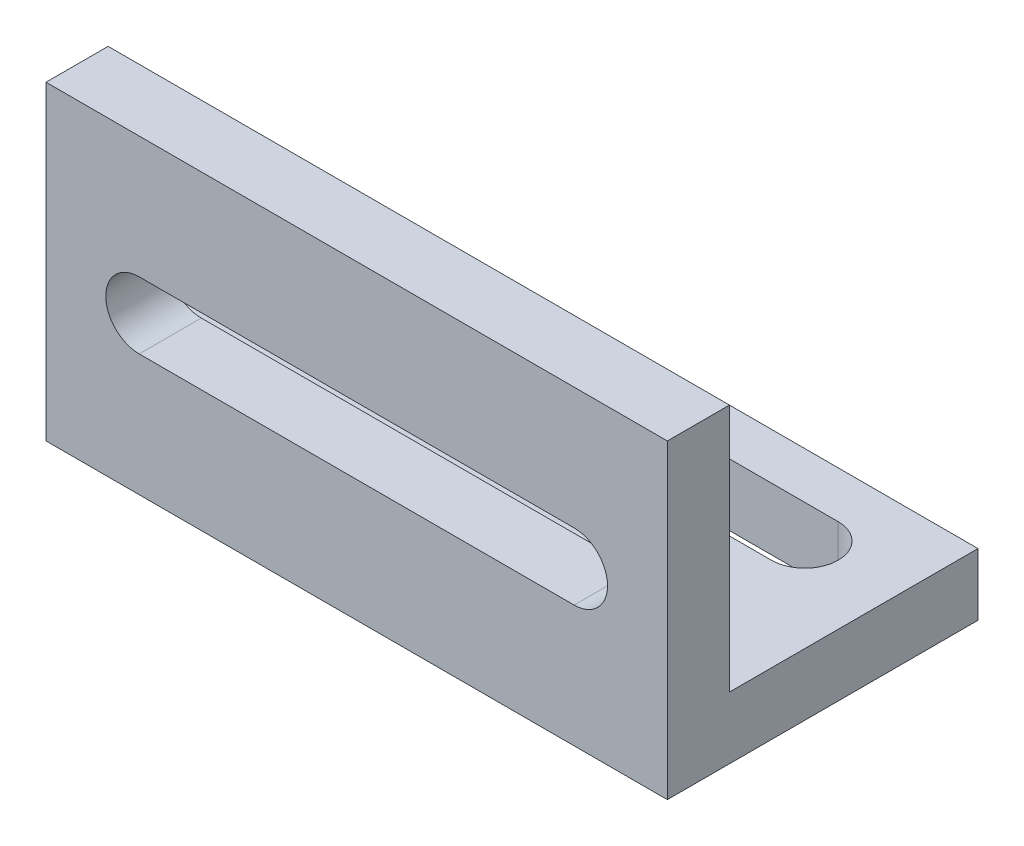
SolidWorks part; units mm, degrees
ref_plane "Front Plane" through (0, 0, 0) normal (0, 0, 1) x (1, 0, 0)
ref_plane "Top Plane" through (0, 0, 0) normal (0, 1, 0) x (1, 0, 0)
ref_plane "Right Plane" through (0, 0, 0) normal (1, 0, 0) x (0, 0, -1)
sketch "Sketch1" plane through (0, 0, 0) normal (0, 1, 0) x (1, 0, 0)
  line L1 (-49.2593, 12.8889) -> (-9.2593, 12.8889)
  line L2 (-49.2593, 12.8889) -> (-49.2593, -7.1111)
  line L4 (-9.2593, 12.8889) -> (-9.2593, -7.1111)
  line L5 (-49.2593, 12.8889) -> (-9.2593, -7.1111) construction
  line L6 (-49.2593, -7.1111) -> (-9.2593, 12.8889) construction
  line L13 (-49.2593, -7.1111) -> (-9.2593, -7.1111)
  line L14 (-49.2593, -7.1111) -> (-49.2593, -3.073)
  line L16 (-9.2593, -7.1111) -> (-9.2593, -3.073)
  point P4 (-29.2593, 2.8889)
  dimension "D1" = 40
  dimension "D2" = 20
extrude "Boss-Extrude1" add sketch "Sketch1" along normal blind 4 contours L2 L13 L4 L1
sketch "Sketch5" plane through (0, 4, 0) normal (0, 1, 0) x (1, 0, 0)
  line L0 (-9.2593, 12.8889) -> (-9.2593, -7.1111) construction
  line L1 (-49.2593, -7.1111) -> (-9.2593, -7.1111)
  line L2 (-49.2593, -7.1111) -> (-49.2593, -3.1111)
  line L3 (-49.2593, -3.1111) -> (-9.2593, -3.1111)
  line L4 (-9.2593, -7.1111) -> (-9.2593, -3.1111)
  line L5 (-49.2593, -7.1111) -> (-9.2593, -3.1111) construction
  line L6 (-49.2593, -3.1111) -> (-9.2593, -7.1111) construction
  point P4 (-29.2593, -5.1111)
  dimension "D1" = 4
extrude "Boss-Extrude2" add sketch "Sketch5" along normal blind 16
sketch "Sketch7" plane through (0, 4, 0) normal (0, 1, 0) x (1, 0, 0)
  line L0 (-49.2593, 12.8889) -> (-9.2593, 12.8889) construction
  line L4 (-15.2593, 7.7389) -> (-43.2593, 7.7389) construction
  line L7 (-15.2593, 5.5889) -> (-43.2593, 5.5889)
  line L8 (-15.2593, 9.8889) -> (-43.2593, 9.8889)
  line L9 (-9.2593, 12.8889) -> (-9.2593, -3.1111) construction
  line L10 (-49.2593, 12.8889) -> (-49.2593, -3.1111) construction
  arc A2 (-15.2593, 5.5889) -> (-15.2593, 9.8889) centre (-15.2593, 7.7389) ccw
  arc A3 (-43.2593, 9.8889) -> (-43.2593, 5.5889) centre (-43.2593, 7.7389) ccw
  point P4 (-29.2593, 12.8889)
  point P8 (-29.2593, 7.7389)
  dimension "D1" = 6
  dimension "D2" = 6
  dimension "D3" = 3
extrude "Cut-Extrude3" cut sketch "Sketch7" against normal blind 10
sketch "Sketch8" plane through (0, 0, 3.1111) normal (0, 0, -1) x (-1, 0, 0)
  line L0 (9.2593, 20) -> (9.2593, 4) construction
  line L2 (49.2593, 20) -> (49.2593, 4) construction
  line L12 (15.2593, 10) -> (43.2593, 10) construction
  line L13 (15.2593, 12.15) -> (43.2593, 12.15)
  line L16 (15.2593, 7.85) -> (43.2593, 7.85)
  arc A8 (15.2593, 12.15) -> (15.2593, 7.85) centre (15.2593, 10) ccw
  arc A9 (43.2593, 7.85) -> (43.2593, 12.15) centre (43.2593, 10) ccw
  point P8 (29.2593, 10)
  dimension "D1" = 6
  dimension "D2" = 6
extrude "Cut-Extrude5" cut sketch "Sketch8" against normal blind 10
